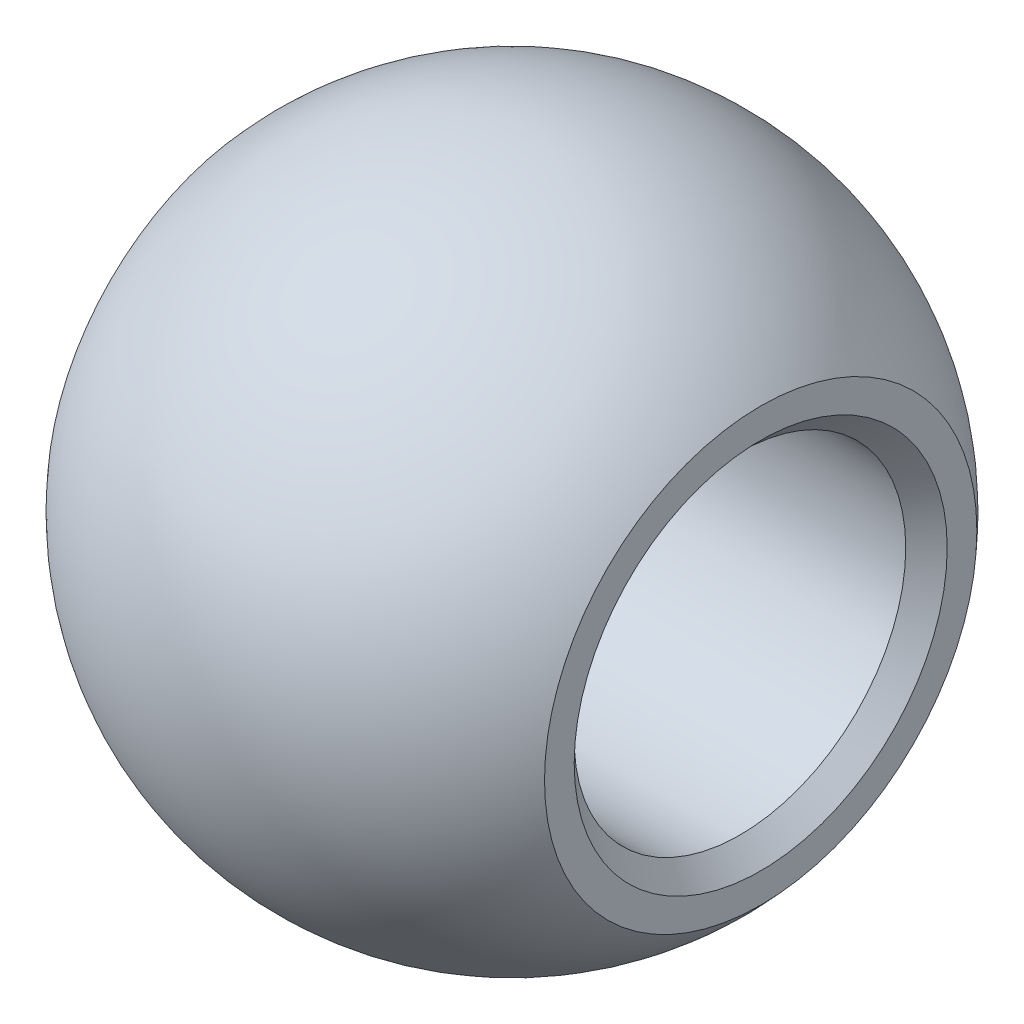
SolidWorks part; units mm, degrees
ref_plane "Front Plane" through (0, 0, 0) normal (0, 0, 1) x (1, 0, 0)
ref_plane "Top Plane" through (0, 0, 0) normal (0, 1, 0) x (1, 0, 0)
ref_plane "Right Plane" through (0, 0, 0) normal (1, 0, 0) x (0, 0, -1)
sketch "Sketch1" plane through (0, 0, 0) normal (0, 0, 1) x (1, 0, 0)
  line L0 (7.95, 0) -> (-7.95, 0) construction
  line L1 (6, 5.2156) -> (6, 4)
  line L2 (6, 4) -> (-6, 4)
  line L3 (-6, 4) -> (-6, 5.2156)
  arc A0 (6, 5.2156) -> (-6, 5.2156) centre (0, 0) ccw
  dimension "D1" = 15.9
  dimension "D2" = 12
  dimension "D3" = 8
revolve "Revolve1" add sketch "Sketch1" angle 360 about L0
chamfer "Chamfer1" distance 0.5 angle 45 2 edges at (-6, 0, -4) (6, 0, -4)
